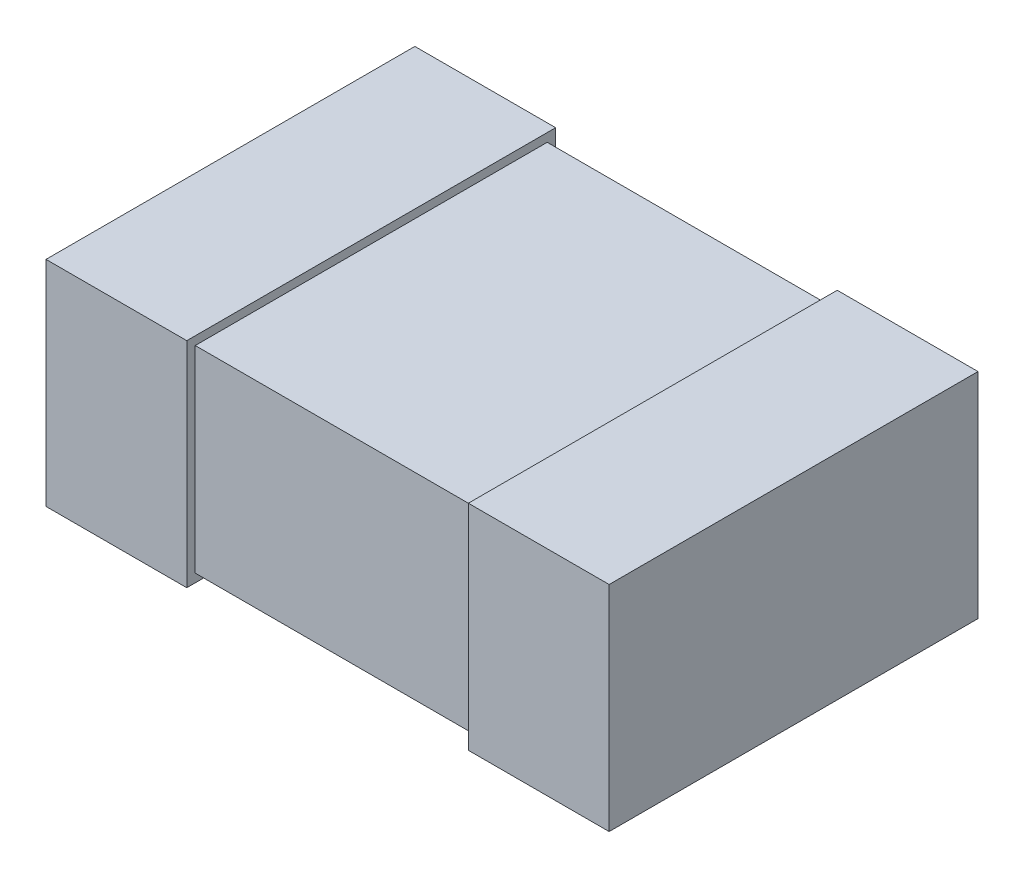
SolidWorks part; units mm, degrees
ref_plane "Front Plane" through (0, 0, 0) normal (0, 0, 1) x (1, 0, 0)
ref_plane "Top Plane" through (0, 0, 0) normal (0, 1, 0) x (1, 0, 0)
ref_plane "Right Plane" through (0, 0, 0) normal (1, 0, 0) x (0, 0, -1)
sketch "Sketch1" plane through (0, 0, 0) normal (0, 1, 0) x (1, 0, 0)
  line L1 (-1, 0.625) -> (1, 0.625)
  line L2 (-1, 0.625) -> (-1, -0.625)
  line L3 (-1, -0.625) -> (1, -0.625)
  line L4 (1, 0.625) -> (1, -0.625)
  point P4 (0, 0.625)
  point P6 (1, 0)
  dimension "D1" = 1.25
  dimension "D2" = 2
extrude "Extrude1" add sketch "Sketch1" along normal blind 0.7
sketch "Sketch2" plane through (0, 0, 0) normal (0, 0, 1) x (1, 0, 0)
  line L0 (-1, 0.7) -> (-1, 0) construction
  line L1 (-0.5, 0.73) -> (-1, 0.73)
  line L2 (-0.5, 0.73) -> (-0.5, -0.03)
  line L3 (-0.5, -0.03) -> (-1, -0.03)
  line L4 (-1, 0.73) -> (-1, -0.03)
  line L5 (-1, 0.7) -> (1, 0.7) construction
  line L6 (-1, 0) -> (1, 0) construction
  line L7 (0, 0) -> (0, -0.3575) construction
  line L8 (1, 0.73) -> (1, -0.03)
  line L9 (0.5, -0.03) -> (1, -0.03)
  line L10 (0.5, 0.73) -> (0.5, -0.03)
  line L11 (0.5, 0.73) -> (1, 0.73)
  dimension "D1" = 0.5
  dimension "D2" = 0.03
  dimension "D3" = 0.03
extrude "Extrude2" add sketch "Sketch2" along normal offset from surface 0.03 and the other way offset from surface (0.655 mm away) 0.03 up to face at (0, 0.35, 0.625) offset beyond the face yes other way up to face at (0, 0.35, -0.625)
ref_plane "Board Plane" through (0, -0.03, 0) normal (0, 1, 0) x (-1, 0, 0)
sketch "Component_Outline" plane through (0, -0.03, 0) normal (0, 1, 0) x (-1, 0, 0)
  line L1 (-1, -0.655) -> (1, -0.655)
  line L2 (-1, -0.655) -> (-1, 0.655)
  line L3 (-1, 0.655) -> (1, 0.655)
  line L4 (1, -0.655) -> (1, 0.655)
